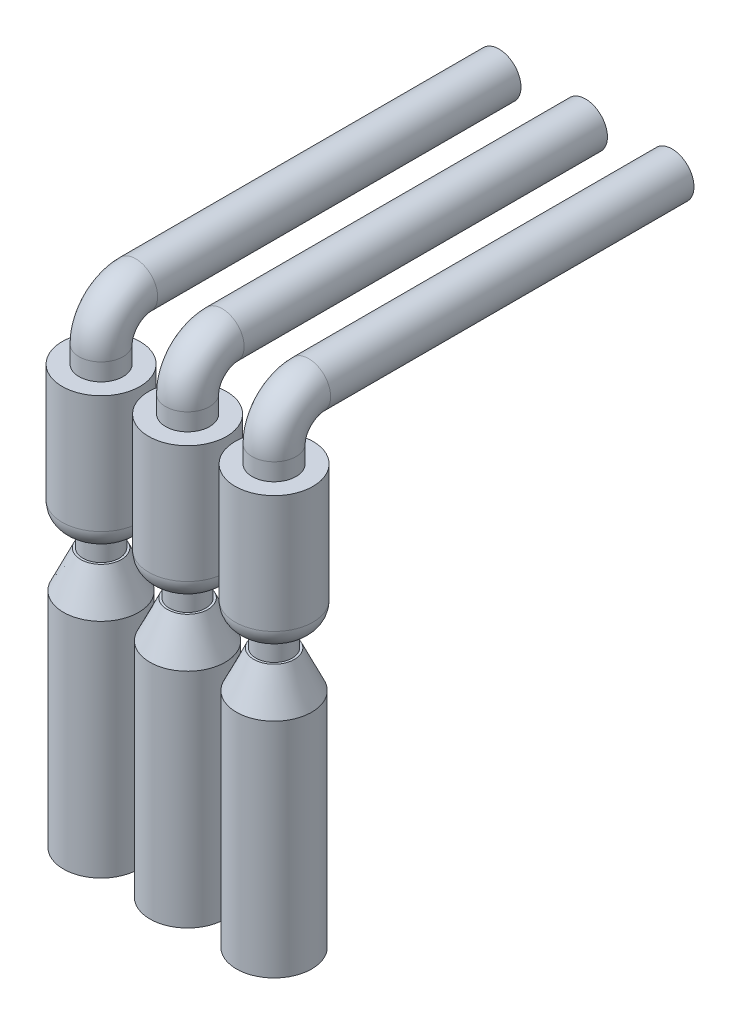
SolidWorks part; units mm, degrees
ref_plane "Alzado" through (0, 0, 0) normal (0, 0, 1) x (1, 0, 0)
ref_plane "Planta" through (0, 0, 0) normal (0, 1, 0) x (1, 0, 0)
ref_plane "Vista lateral" through (0, 0, 0) normal (1, 0, 0) x (0, 0, -1)
sketch "Croquis1" plane through (0, 0, 0) normal (0, 0, 1) x (1, 0, 0)
  circle A0 centre (0, 0) radius 127
  circle A1 centre (500, 0) radius 127
  circle A2 centre (1000, 0) radius 127
  dimension "D1" = 254
  dimension "D2" = 254
  dimension "D3" = 254
  dimension "D4" = 500
  dimension "D5" = 500
extrude "Saliente-Extruir1" add sketch "Croquis1" along normal blind 2000
sketch3d "Croquis3D1"
  line L0 (0, 0, 2000) -> (0, 0, 2100)
  line L1 (0, 0, 2000) -> (0, 0, 0) construction
  line L2 (0, -200, 2300) -> (0, -300, 2300)
  arc A0 (0, 0, 2100) -> (0, -200, 2300) centre (0, -200, 2100) ccw
  point P7 (0, 0, 2300)
  point P8 (200, -200, 2100)
  dimension "D3" = 200
  dimension "D1" = 300
  dimension "D2" = 300
sketch "Croquis3" plane through (0, 0, 2000) normal (0, 0, 1) x (1, 0, 0)
  circle A0 centre (0, 0) radius 127
sweep "Barrer1" add profiles "Croquis3" path "Croquis3D1"
sketch3d "Croquis3D2"
  line L0 (500, 0, 2000) -> (500, 0, 2100)
  line L1 (500, 0, 2000) -> (500, 0, 0) construction
  line L2 (500, -200, 2300) -> (500, -300, 2300)
  arc A0 (500, 0, 2100) -> (500, -200, 2300) centre (500, -200, 2100) ccw
  point P7 (500, 0, 2300)
  point P8 (700, -200, 2100)
  dimension "D3" = 200
  dimension "D1" = 300
  dimension "D2" = 300
sketch "Croquis5" plane through (0, 0, 2000) normal (0, 0, 1) x (1, 0, 0)
  circle A0 centre (500, 0) radius 127
sweep "Barrer2" add profiles "Croquis5" path "Croquis3D2"
sketch3d "Croquis3D4"
  line L0 (1000, 0, 2000) -> (1000, 0, 2100)
  line L1 (1000, 0, 2000) -> (1000, 0, 0) construction
  line L2 (1000, -200, 2300) -> (1000, -300, 2300)
  arc A0 (1000, 0, 2100) -> (1000, -200, 2300) centre (1000, -200, 2100) ccw
  point P7 (1000, 0, 2300)
  point P8 (1200, -200, 2100)
  dimension "D3" = 200
  dimension "D1" = 300
  dimension "D2" = 300
sketch "Croquis6" plane through (0, 0, 2000) normal (0, 0, 1) x (1, 0, 0)
  circle A0 centre (1000, 0) radius 127
sweep "Barrer3" add profiles "Croquis6" path "Croquis3D4"
sketch "Croquis7" plane through (0, -300, 0) normal (0, -1, 0) x (1, 0, 0)
  circle A0 centre (0, 2300) radius 225
  circle A1 centre (500, 2300) radius 225
  circle A2 centre (1000, 2300) radius 225
  dimension "D1" = 450
  dimension "D2" = 450
  dimension "D3" = 450
extrude "Saliente-Extruir2" add sketch "Croquis7" along normal blind 800
fillet "Redondeo1" radius 120 1 edges at (1225, -1100, 2300)
fillet "Redondeo2" radius 120 1 edges at (725, -1100, 2300)
fillet "Redondeo3" radius 120 1 edges at (225, -1100, 2300)
sketch "Croquis8" plane through (0, -1100, 0) normal (0, -1, 0) x (1, 0, 0)
  circle A0 centre (1000, 2300) radius 105
  circle A1 centre (500, 2300) radius 105
  circle A2 centre (0, 2300) radius 105
extrude "Saliente-Extruir3" add sketch "Croquis8" along normal blind 120
sketch "Croquis9" plane through (0, -1220, 0) normal (0, -1, 0) x (1, 0, 0)
  circle A0 centre (1000, 2300) radius 217.5
  circle A1 centre (500, 2300) radius 217.5
  circle A2 centre (0, 2300) radius 217.5
  dimension "D1" = 435
  dimension "D2" = 435
  dimension "D3" = 435
extrude "Saliente-Extruir4" add sketch "Croquis9" along normal blind 1500
chamfer "Chaflán1" distance 100 angle 65 1 edges at (1217.5, -1220, 2300)
chamfer "Chaflán2" distance 100 angle 65 1 edges at (717.5, -1220, 2300)
chamfer "Chaflán3" distance 100 angle 65 1 edges at (217.5, -1220, 2300)
